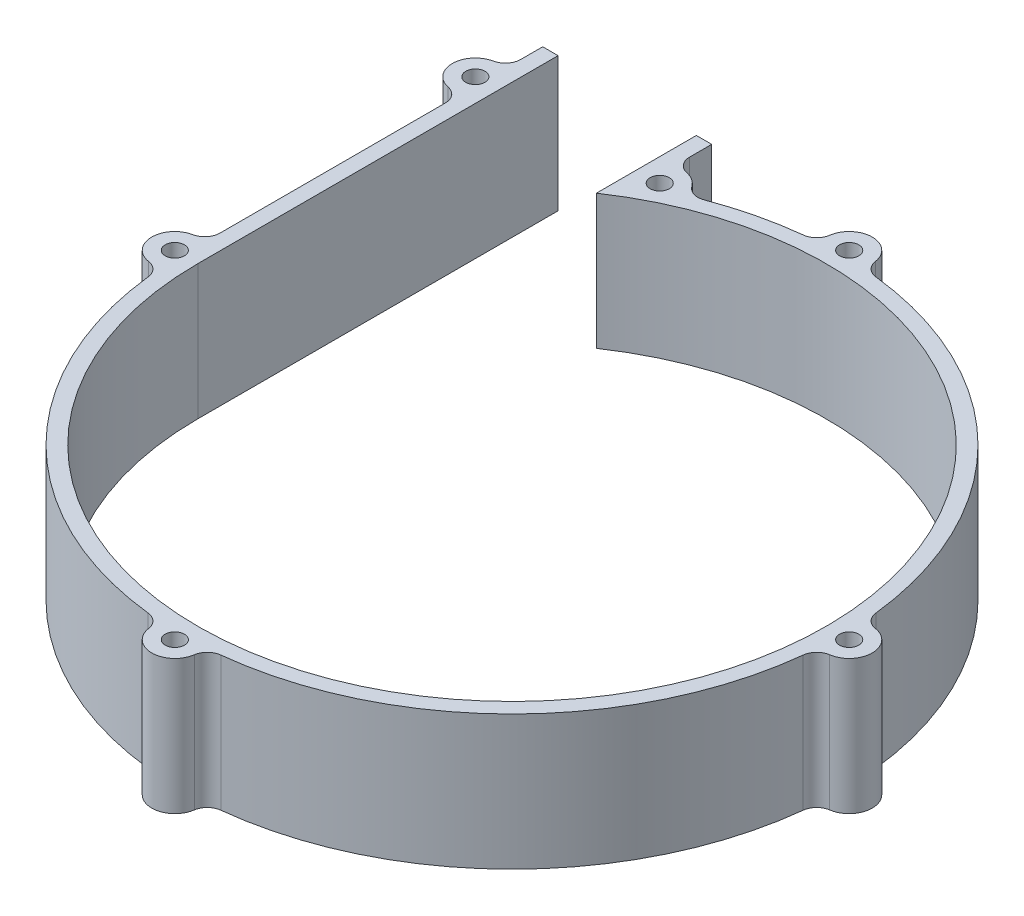
SolidWorks part; units mm, degrees
material "6061 合金"
ref_plane "前视基准面" through (0, 0, 0) normal (0, 0, 1) x (1, 0, 0)
ref_plane "上视基准面" through (0, 0, 0) normal (0, 1, 0) x (1, 0, 0)
ref_plane "右视基准面" through (0, 0, 0) normal (1, 0, 0) x (0, 0, -1)
sketch "草图1" plane through (0, 0, 0) normal (0, 1, 0) x (1, 0, 0)
  line L0 (-31.9, 0) -> (-31.9, 46.9) construction
  line L1 (-40.9, 0) -> (-40.9, 46.9)
  line L2 (-22.9, 46.9) -> (-22.9, 33.8881)
  line L3 (-40.9, 46.9) -> (-42.9, 46.9)
  line L4 (-42.9, 46.9) -> (-42.9, 44.0295)
  line L5 (-43.9, 0) -> (-43.9, 46.9) construction
  line L6 (-19.9, 39.1306) -> (-19.9, 46.9) construction
  line L7 (-20.9, 46.9) -> (-20.9, 44.0295)
  line L8 (-22.9, 46.9) -> (-20.9, 46.9)
  line L9 (-20.9, 46.9) -> (-20.9, 33.8881) construction
  line L10 (-42.9, 34.2316) -> (-42.9, 4.899)
  arc A0 (-40.9, 0) -> (-22.9, 33.8881) centre (0, 0) ccw
  circle A1 centre (0, 0) radius 43.9 construction
  circle A2 centre (0, 0) radius 31.9 construction
  circle A4 centre (0, 0) radius 40.9 construction
  circle A5 centre (0, 43.9) radius 1.25
  circle A6 centre (43.9, 0) radius 1.25
  circle A7 centre (0, -43.9) radius 1.25
  circle A8 centre (-43.9, 0) radius 1.25
  arc A9 (2.9681, 44.336) -> (-2.9681, 44.336) centre (0, 43.9) ccw
  arc A10 (44.336, -2.9681) -> (44.336, 2.9681) centre (43.9, 0) ccw
  arc A11 (-2.9681, -44.336) -> (2.9681, -44.336) centre (0, -43.9) ccw
  arc A12 (-44.5, 2.9394) -> (-44.336, -2.9681) centre (-43.9, 0) ccw
  arc A14 (-42.6388, -4.7266) -> (-4.7266, -42.6388) centre (0, 0) ccw
  arc A15 (4.7266, -42.6388) -> (42.6388, -4.7266) centre (0, 0) ccw
  arc A16 (42.6388, 4.7266) -> (4.7266, 42.6388) centre (0, 0) ccw
  arc A17 (-4.7266, 42.6388) -> (-15.1153, 40.149) centre (0, 0) ccw
  circle A18 centre (-19.9, 39.1306) radius 1.25
  arc A19 (-17.452, 40.8646) -> (-19.3, 42.0699) centre (-19.9, 39.1306) ccw
  circle A20 centre (-43.9, 39.1306) radius 1.25
  arc A21 (-44.5, 42.0699) -> (-44.5, 36.1912) centre (-43.9, 39.1306) ccw
  arc A22 (-44.336, -2.9681) -> (-42.6388, -4.7266) centre (-44.6267, -4.9469) cw
  arc A23 (-44.5, 2.9394) -> (-42.9, 4.899) centre (-44.9, 4.899) ccw
  arc A24 (2.9681, -44.336) -> (4.7266, -42.6388) centre (4.9469, -44.6267) cw
  arc A25 (-2.9681, -44.336) -> (-4.7266, -42.6388) centre (-4.9469, -44.6267) ccw
  arc A26 (44.336, -2.9681) -> (42.6388, -4.7266) centre (44.6267, -4.9469) ccw
  arc A27 (44.336, 2.9681) -> (42.6388, 4.7266) centre (44.6267, 4.9469) cw
  arc A28 (2.9681, 44.336) -> (4.7266, 42.6388) centre (4.9469, 44.6267) ccw
  arc A29 (-4.7266, 42.6388) -> (-2.9681, 44.336) centre (-4.9469, 44.6267) ccw
  arc A30 (-17.452, 40.8646) -> (-15.1153, 40.149) centre (-15.8199, 42.0207) ccw
  arc A31 (-19.3, 42.0699) -> (-20.9, 44.0295) centre (-18.9, 44.0295) cw
  arc A32 (-44.5, 36.1912) -> (-42.9, 34.2316) centre (-44.9, 34.2316) cw
  arc A33 (-44.5, 42.0699) -> (-42.9, 44.0295) centre (-44.9, 44.0295) ccw
  circle A34 centre (0, 0) radius 46.9 construction
  point P11 (0, 46.9)
  point P52 (2.7945, -42.8089)
  point P59 (42.8089, 2.7945)
  point P70 (-42.9, 36.3021)
  dimension "D1" = 81.8
  dimension "D3" = 9
  dimension "D6" = 2.5
  dimension "D8" = 6
  dimension "D12" = 2
  dimension "D13" = 2
  dimension "D5" = 9
  dimension "D10" = 3
  dimension "D9" = 2
  dimension "D2" = 3
  dimension "D4" = 4
  dimension "D11" = 2
  dimension "D14" = 3
  dimension "D7" = 4
extrude "凸台-拉伸1" add sketch "草图1" along normal blind 17.5
cosmetic thread "装饰螺纹线1" parameters "D2"=3
cosmetic thread "装饰螺纹线2" parameters "D2"=3
cosmetic thread "装饰螺纹线3" parameters "D2"=3
cosmetic thread "装饰螺纹线4" parameters "D2"=3
cosmetic thread "装饰螺纹线5" parameters "D2"=3
cosmetic thread "装饰螺纹线6" parameters "D2"=3
